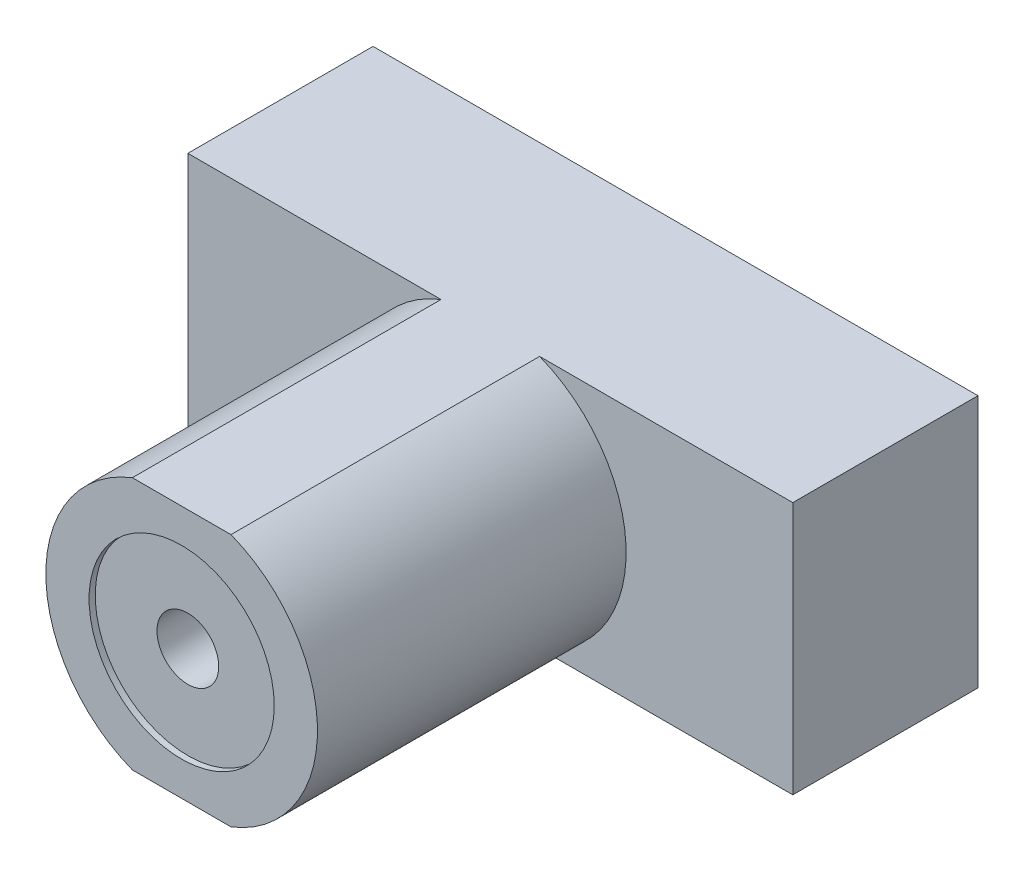
SolidWorks part; units mm, degrees
ref_plane "Front" through (0, 0, 0) normal (0, 0, 1) x (1, 0, 0)
ref_plane "Top" through (0, 0, 0) normal (0, 1, 0) x (1, 0, 0)
ref_plane "Right" through (0, 0, 0) normal (1, 0, 0) x (0, 0, -1)
sketch "COMPONENT_OUTLINE" plane through (0, 0, 0) normal (0, 0, 1) x (1, 0, 0)
  line L0 (-4.9, -5.5) -> (4.9, -5.5)
  line L1 (4.9, -5.5) -> (4.9, -1.4)
  line L2 (4.9, -1.4) -> (-4.9, -1.4)
  line L3 (-4.9, -1.4) -> (-4.9, -5.5)
extrude "Extrude1" add sketch "COMPONENT_OUTLINE" along normal blind 8
sketch "Sketch1" plane through (0, 0, 8) normal (0, 0, 1) x (1, 0, 0)
  line L0 (0.7984, -5.5) -> (4.9, -5.5)
  line L1 (-0.7984, -1.4) -> (-4.9, -1.4)
  line L2 (0, -1.4) -> (0, -5.5) construction
  line L3 (4.9, -1.4) -> (-4.9, -1.4) construction
  line L4 (-4.9, -1.4) -> (-4.9, -5.5)
  line L5 (-4.9, -5.5) -> (4.9, -5.5)
  line L6 (4.9, -5.5) -> (4.9, -1.4)
  line L7 (4.9, -1.4) -> (-4.9, -1.4)
  line L8 (-4.9, -1.4) -> (-4.9, -5.5)
  line L9 (-4.9, -5.5) -> (-0.7984, -5.5)
  line L10 (4.9, -5.5) -> (4.9, -1.4)
  line L11 (4.9, -1.4) -> (0.7984, -1.4)
  line L12 (-4.9, -5.5) -> (4.9, -5.5) construction
  arc A0 (0.7984, -5.5) -> (0.7984, -1.4) centre (0, -3.45) ccw
  arc A1 (-0.7984, -1.4) -> (-0.7984, -5.5) centre (0, -3.45) ccw
  dimension "D2" = 2.2
  dimension "D1" = 0
extrude "Cut-Extrude1" cut sketch "Sketch1" against normal blind 5
sketch "Sketch3" plane through (0, 0, 8) normal (0, 0, 1) x (1, 0, 0)
  circle A0 centre (0, -3.45) radius 0.5
  arc A1 (-0.7984, -1.4) -> (-0.7984, -5.5) centre (0, -3.45) ccw construction
  dimension "D1" = 1
extrude "Cut-Extrude2" cut sketch "Sketch3" against normal blind 5
sketch "Sketch4" plane through (0, 0, 8) normal (0, 0, 1) x (1, 0, 0)
  circle A2 centre (0, -3.45) radius 1.5
  circle A3 centre (0, -3.45) radius 1.5
  dimension "D1" = 1
extrude "Cut-Extrude3" cut sketch "Sketch4" against normal blind 0.1
